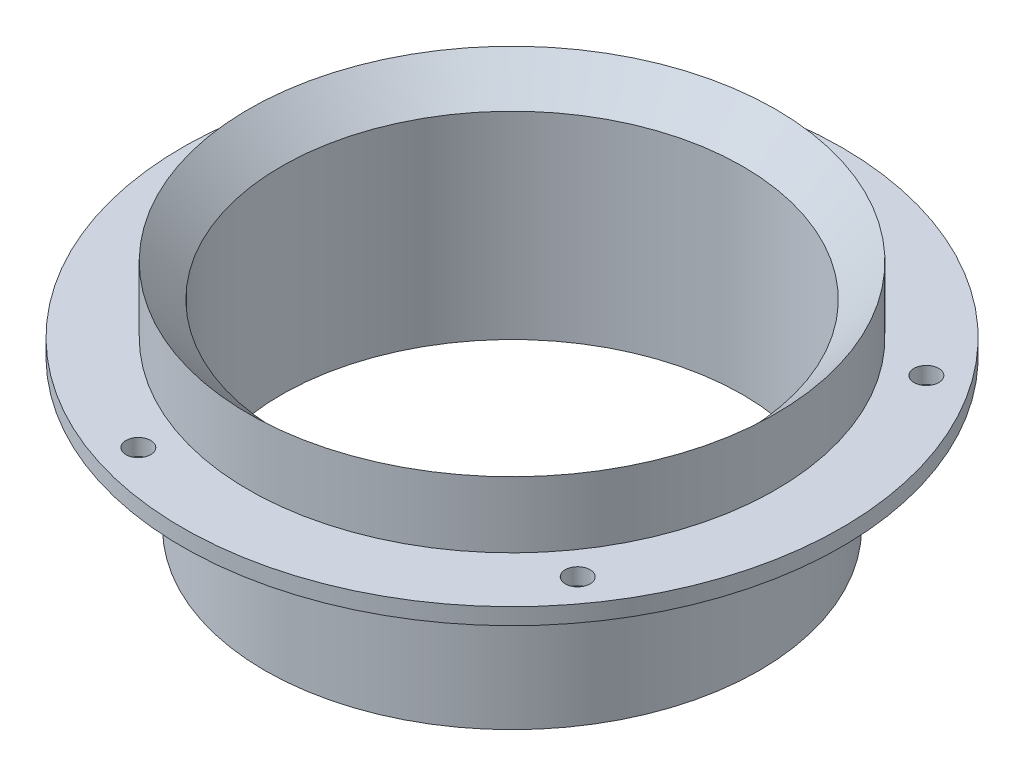
SolidWorks part; units mm, degrees
ref_plane "Front Plane" through (0, 0, 0) normal (0, 0, 1) x (1, 0, 0)
ref_plane "Top Plane" through (0, 0, 0) normal (0, 1, 0) x (1, 0, 0)
ref_plane "Right Plane" through (0, 0, 0) normal (1, 0, 0) x (0, 0, -1)
sketch "Sketch2" plane through (0, 0, 0) normal (0, 0, 1) x (1, 0, 0)
  line L0 (0, 0) -> (-88.9, 0) construction
  line L1 (0, 3.7259) -> (0, 51448.5004) construction
  line L2 (-88.9, 0) -> (-95.25, 0)
  line L3 (-95.25, 0) -> (-95.25, 57.15)
  line L4 (-95.25, 57.15) -> (-127, 57.15)
  line L5 (-127, 57.15) -> (-127, 63.5)
  line L6 (-127, 63.5) -> (-101.6, 63.5)
  line L7 (-101.6, 63.5) -> (-101.6, 88.9)
  line L8 (-101.6, 88.9) -> (-88.9, 76.2)
  line L9 (-88.9, 0) -> (-88.9, 76.2)
  point P3 (-49.6539, 40.6812)
  dimension "D1" = 76.2
  dimension "D2" = 88.9
  dimension "D3" = 6.35
  dimension "D4" = 6.35
  dimension "D5" = 25.4
  dimension "D6" = 12.7
  dimension "D7" = 45
  dimension "D8" = 25.4
revolve "Revolve1" add sketch "Sketch2" angle 360 about L1
sketch "Sketch3" plane through (0, 63.5, 0) normal (0, 1, 0) x (1, 0, 0)
  line L0 (0, 0) -> (-114.3, 0) construction
  point P4 (-114.3, 0)
  dimension "D1" = 114.3
hole_wizard "Hole1" positions "Sketch3" profile "Sketch4" legacy end condition through all
sketch "Sketch4" plane through (-114.3, 63.5, 0) normal (1, 0, 0) x (0, 0, 1)
  line L0 (0, 0) -> (0, 63.5)
  line L1 (0, 63.5) -> (4.7625, 63.5)
  line L2 (4.7625, 63.5) -> (4.7625, 0)
  line L3 (4.7625, 0) -> (0, 0)
  line L4 (0, 110) -> (0, -10) construction
  dimension "Diameter" = 9.525
  dimension "Depth" = 63.5
pattern_circular "CirPattern1" count 5 over 360 about axis through (0, 0, 0) along (0, 1, 0) of "Hole1"
equation "\"l_shroud\" = 3in"
equation "\"d_shroud\"= 7in"
equation "\"t_wall\" = 0.25in"
equation "\"D1@Sketch2\"=\"l_shroud\""
equation "\"D2@Sketch2\"=\"d_shroud\"/2"
equation "\"D3@Sketch2\"=\"t_wall\""
equation "\"t_flange\" = 0.25in"
equation "\"t_ext\"= 0.5in"
equation "\"l_ext\" = 1in"
equation "\"D4@Sketch2\"=\"t_flange\""
equation "\"D5@Sketch2\"=\"l_ext\""
equation "\"D6@Sketch2\"=\"t_ext\""
equation "\"l_flange\"= 1in"
equation "\"D8@Sketch2\"=\"l_flange\""
equation "\"d_mount\"= 4.5in"
equation "\"d_bolt\"= 0.375in"
equation "\"D1@Sketch3\"=\"d_mount\""
equation "\"Diameter@Sketch4\"=\"d_bolt\""
equation "\"num_bolts\"= 5"
equation "\"D1@CirPattern1\"=\"num_bolts\""
